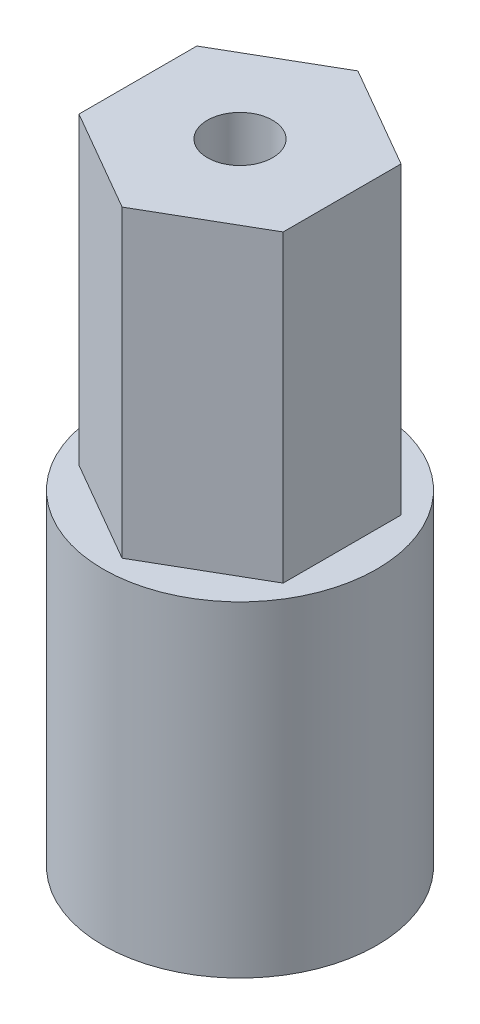
SolidWorks part; units mm, degrees
ref_plane "Front Plane" through (0, 0, 0) normal (0, 0, 1) x (1, 0, 0)
ref_plane "Top Plane" through (0, 0, 0) normal (0, 1, 0) x (1, 0, 0)
ref_plane "Right Plane" through (0, 0, 0) normal (1, 0, 0) x (0, 0, -1)
sketch "Sketch1" plane through (0, 0, 0) normal (0, 1, 0) x (1, 0, 0)
  circle A2 centre (0, 0) radius 8.001
  dimension "D3" = 16.002
extrude "Boss-Extrude1" add sketch "Sketch1" along normal blind 6.35
sketch "Sketch3" plane through (0, 0, 0) normal (0, -1, 0) x (-1, 0, 0)
  circle A0 centre (0, 0) radius 8.001
  circle A1 centre (0, 0) radius 8.001 construction
  dimension "D1" = 0
extrude "Boss-Extrude2" add sketch "Sketch3" along normal blind 12.7
sketch "Sketch4" plane through (0, -12.7, 0) normal (0, -1, 0) x (1, 0, 0)
  line L0 (0, 2.794) -> (-1.9757, 4.7696)
  line L1 (-2.794, -2.794) -> (2.794, -2.794) construction
  line L2 (-2.794, -2.794) -> (-2.794, 2.794) construction
  line L3 (-2.794, 2.794) -> (2.794, 2.794) construction
  line L4 (2.794, -2.794) -> (2.794, 2.794) construction
  line L5 (-2.794, -2.794) -> (2.794, 2.794) construction
  line L6 (-2.794, 2.794) -> (2.794, -2.794) construction
  line L7 (-2.794, 0) -> (-4.7697, 1.9756)
  line L8 (-4.7697, 1.9756) -> (-1.9757, 4.7696)
  line L9 (2.794, 0) -> (4.7697, -1.9757)
  line L10 (0, -2.794) -> (1.9757, -4.7697)
  line L11 (1.9757, -4.7697) -> (4.7697, -1.9757)
  line L12 (-2.794, 0) -> (-4.7697, -1.9757)
  line L13 (0, -2.794) -> (-1.9757, -4.7697)
  line L14 (-4.7697, -1.9757) -> (-1.9757, -4.7697)
  line L15 (2.794, 0) -> (4.7697, 1.9757)
  line L16 (1.9756, 4.7697) -> (4.7697, 1.9757)
  line L17 (0, 2.794) -> (1.9756, 4.7697)
  point P0 (0, 0)
extrude "Cut-Extrude1" cut sketch "Sketch4" against normal blind 12.7
sketch "Sketch11" plane through (0, 6.35, 0) normal (0, 1, 0) x (1, 0, 0)
  line L0 (0, 6.8924) -> (-5.969, 3.4462)
  line L1 (-5.969, 3.4462) -> (-5.969, -3.4462)
  line L2 (-5.969, -3.4462) -> (0, -6.8924)
  line L3 (0, -6.8924) -> (5.969, -3.4462)
  line L4 (5.969, -3.4462) -> (5.969, 3.4462)
  line L5 (5.969, 3.4462) -> (0, 6.8924)
  circle A0 centre (0, 0) radius 5.969 construction
  circle A1 centre (0, 0) radius 1.905
  dimension "D1" = 11.938
  dimension "D2" = 3.81
extrude "Boss-Extrude5" add sketch "Sketch11" along normal blind 17.78
